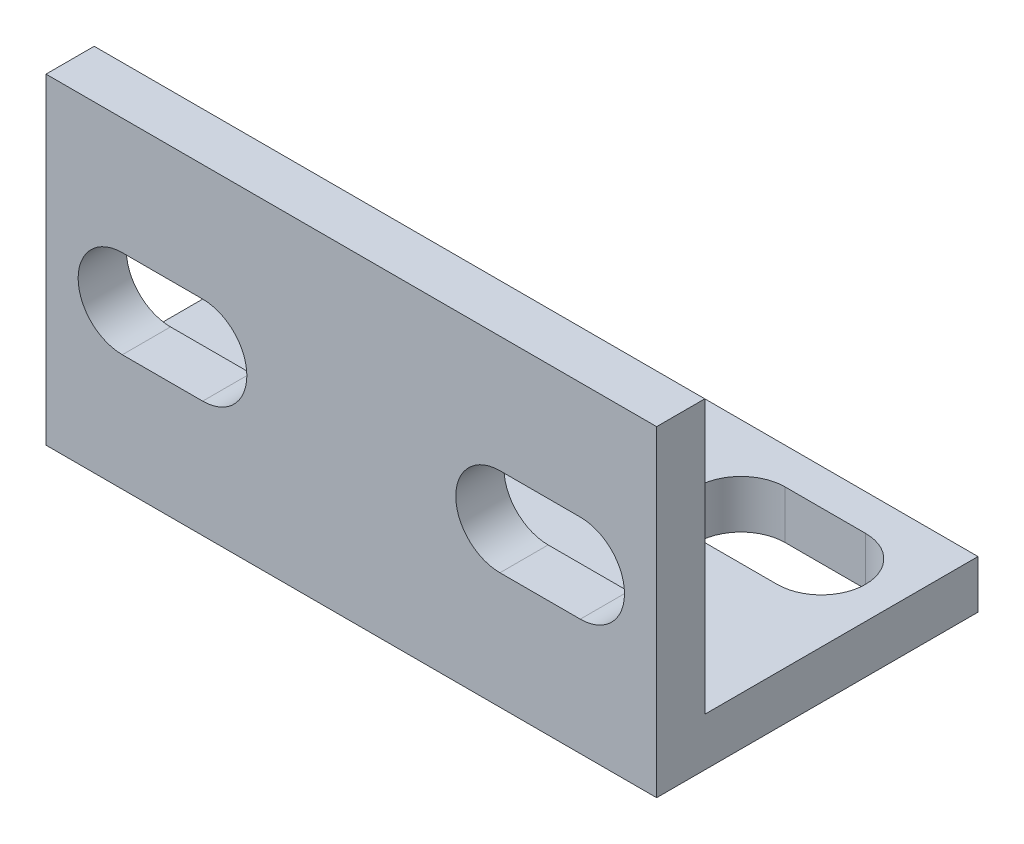
SolidWorks part; units mm, degrees
ref_plane "Front Plane" through (0, 0, 0) normal (0, 0, 1) x (1, 0, 0)
ref_plane "Top Plane" through (0, 0, 0) normal (0, 1, 0) x (1, 0, 0)
ref_plane "Right Plane" through (0, 0, 0) normal (1, 0, 0) x (0, 0, -1)
sketch "Sketch1" plane through (0, 0, 0) normal (1, 0, 0) x (0, 0, -1)
  line L0 (0, 20) -> (0, 0)
  line L1 (0, 0) -> (20, 0)
  line L2 (20, 0) -> (20, 3)
  line L3 (20, 3) -> (3, 3)
  line L4 (3, 3) -> (3, 20)
  line L5 (3, 20) -> (0, 20)
  dimension "D1" = 20
  dimension "D2" = 20
  dimension "D3" = 3
  dimension "D4" = 3
extrude "Boss-Extrude1" add sketch "Sketch1" against normal blind 38
sketch "Sketch2" plane through (0, 0, -3) normal (0, 0, -1) x (-1, 0, 0)
  line L0 (19, 20) -> (19, 3) construction
  line L1 (38, 20) -> (0, 20) construction
  line L2 (38, 3) -> (0, 3) construction
  line L3 (4.75, 10) -> (9.75, 10) construction
  line L4 (4.75, 12.75) -> (9.75, 12.75)
  line L5 (4.75, 7.25) -> (9.75, 7.25)
  line L6 (7.25, 20) -> (7.25, 3) construction
  line L7 (0, 3) -> (0, 20) construction
  line L8 (7.25, 10) -> (0, 10) construction
  arc A0 (4.75, 12.75) -> (4.75, 7.25) centre (4.75, 10) ccw
  arc A1 (9.75, 7.25) -> (9.75, 12.75) centre (9.75, 10) ccw
  point P8 (7.25, 10)
  dimension "D3" = 7.25
  dimension "D1" = 5.5
  dimension "D2" = 5
  dimension "D4" = 11.75
extrude "Cut-Extrude1" cut sketch "Sketch2" against normal through all contours L4 A1 L5 A0
sketch "Sketch3" plane through (0, 3, 0) normal (0, 1, 0) x (1, 0, 0)
  line L0 (-19, 3) -> (-19, 20) construction
  line L1 (-38, 3) -> (0, 3) construction
  line L2 (-38, 20) -> (0, 20) construction
  line L3 (-4.75, 15) -> (-9.75, 15) construction
  line L4 (-4.75, 12.25) -> (-9.75, 12.25)
  line L5 (-4.75, 17.75) -> (-9.75, 17.75)
  line L6 (-19, 15) -> (0, 15) construction
  line L7 (0, 20) -> (0, 3) construction
  arc A0 (-4.75, 12.25) -> (-4.75, 17.75) centre (-4.75, 15) ccw
  arc A1 (-9.75, 17.75) -> (-9.75, 12.25) centre (-9.75, 15) ccw
  point P8 (-7.25, 15)
  dimension "D1" = 5.5
  dimension "D2" = 5
  dimension "D3" = 2.25
  dimension "D4" = 11.75
extrude "Cut-Extrude2" cut sketch "Sketch3" against normal through all
ref_plane "Plane1" through (-19, 0, 0) normal (1, 0, 0) x (0, 0, -1)
mirror "Mirror1" about plane through (-19, 0, 0) normal (1, 0, 0) of "Cut-Extrude1"
mirror "Mirror2" about plane through (-19, 0, 0) normal (1, 0, 0) of "Cut-Extrude2"
